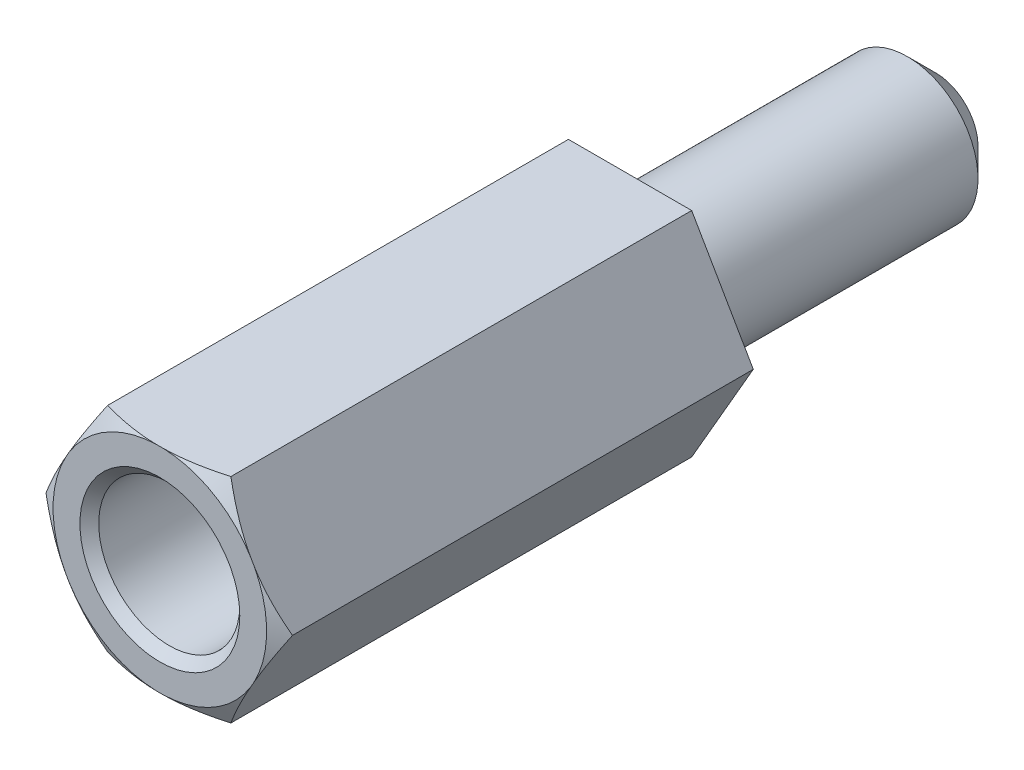
SolidWorks part; units mm, degrees
ref_plane "Front Plane" through (0, 0, 0) normal (0, 0, 1) x (1, 0, 0)
ref_plane "Top Plane" through (0, 0, 0) normal (0, 1, 0) x (1, 0, 0)
ref_plane "Right Plane" through (0, 0, 0) normal (1, 0, 0) x (0, 0, -1)
sketch "Sketch1" plane through (0, 0, 0) normal (0, 0, 1) x (1, 0, 0)
  line L0 (0, 0) -> (2.6212, 0) construction
  line L1 (2.6212, 0) -> (1.3106, 2.27)
  line L2 (1.3106, 2.27) -> (-1.3106, 2.27)
  line L3 (-1.3106, 2.27) -> (-2.6212, 0)
  line L4 (-2.6212, 0) -> (-1.3106, -2.27)
  line L5 (-1.3106, -2.27) -> (1.3106, -2.27)
  line L6 (1.3106, -2.27) -> (2.6212, 0)
  circle A0 centre (0, 0) radius 2.27 construction
  dimension "D1" = 4.54
extrude "Boss-Extrude1" add sketch "Sketch1" along normal blind 10
sketch "Sketch2" plane through (0, 0, 10) normal (0, 0, 1) x (1, 0, 0)
  circle A0 centre (0, 0) radius 1.5
extrude "Cut-Extrude1" cut sketch "Sketch2" against normal blind 9 and the other way through all
sketch "Sketch3" plane through (0, 0, 0) normal (0, 1, 0) x (1, 0, 0)
  line L0 (-2.6212, -10) -> (-2.2712, -10)
  line L1 (-2.2712, -10) -> (-2.6212, -9.8)
  line L2 (-2.6212, -10) -> (-2.6212, 0) construction
  line L3 (-2.6212, -9.8) -> (-2.6212, -10)
  dimension "D1" = 0.35
  dimension "D2" = 0.2
ref_axis "Axis1" through (0, 0, 1) along (0, 0, 1)
revolve "Cut-Revolve1" cut sketch "Sketch3" angle 360 about axis through (0, 0, 1) along (0, 0, 1)
ref_plane "Plane1" through (0, 0, 5) normal (0, 0, 1) x (1, 0, 0)
chamfer "Chamfer1" distance 0.2 angle 45 1 edges at (1.5, 0, 10)
sketch "Sketch4" plane through (0, 0, 0) normal (0, 0, -1) x (-1, 0, 0)
  circle A0 centre (0, 0) radius 1.5
extrude "Boss-Extrude2" add sketch "Sketch4" along normal blind 6.5
chamfer "Chamfer2" distance 0.6 angle 45 1 edges at (-1.5, 0, -6.5)
